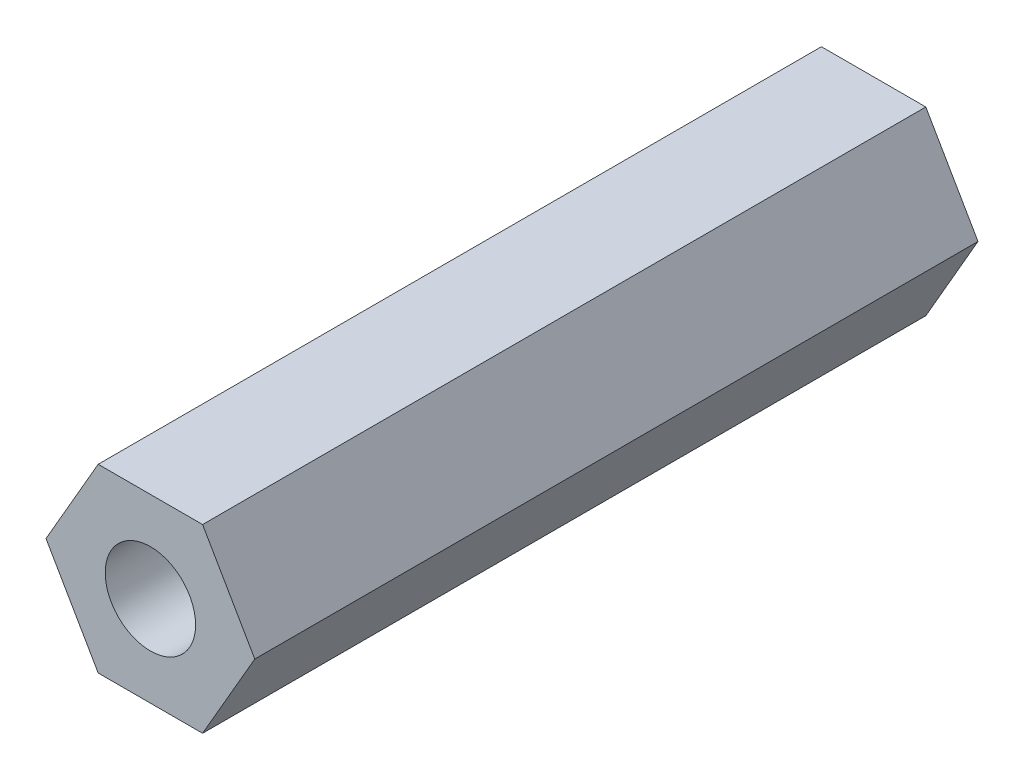
SolidWorks part; units mm, degrees
material "黃銅"
ref_plane "前基準面" through (0, 0, 0) normal (0, 0, 1) x (1, 0, 0)
ref_plane "上基準面" through (0, 0, 0) normal (0, 1, 0) x (1, 0, 0)
ref_plane "右基準面" through (0, 0, 0) normal (1, 0, 0) x (0, 0, -1)
sketch "草圖1" plane through (0, 0, 0) normal (0, 0, 1) x (1, 0, 0)
  line L1 (-1.4434, 2.5) -> (-2.8868, 0)
  line L2 (-2.8868, 0) -> (-1.4434, -2.5)
  line L3 (-1.4434, -2.5) -> (1.4434, -2.5)
  line L4 (1.4434, -2.5) -> (2.8868, 0)
  line L5 (2.8868, 0) -> (1.4434, 2.5)
  line L6 (1.4434, 2.5) -> (-1.4434, 2.5)
  circle A0 centre (0, 0) radius 2.5 construction
  dimension "D1" = 5
extrude "填料-伸長1" add sketch "草圖1" along normal blind 20
hole_wizard "M3x0.5 螺紋孔1" positions "草圖2" profile "草圖3" tap size "M3x0.5" standard "Ansi Metric" end condition through all
sketch "草圖2" plane through (0, 0, 20) normal (0, 0, 1) x (1, 0, 0)
  point P0 (0, 0)
sketch "草圖3" plane through (0, 0, 20) normal (1, 0, 0) x (0, -1, 0)
  line L0 (0, 0) -> (0, 20)
  line L1 (0, 20) -> (1.25, 20)
  line L2 (1.25, 20) -> (1.25, 0)
  line L5 (1.25, 0) -> (0, 0)
  line L11 (0, -6.35) -> (0, 107.95) construction
  dimension "貫穿螺孔鑽直徑" = 2.5
  dimension "貫穿螺孔鑽深度" = 20
